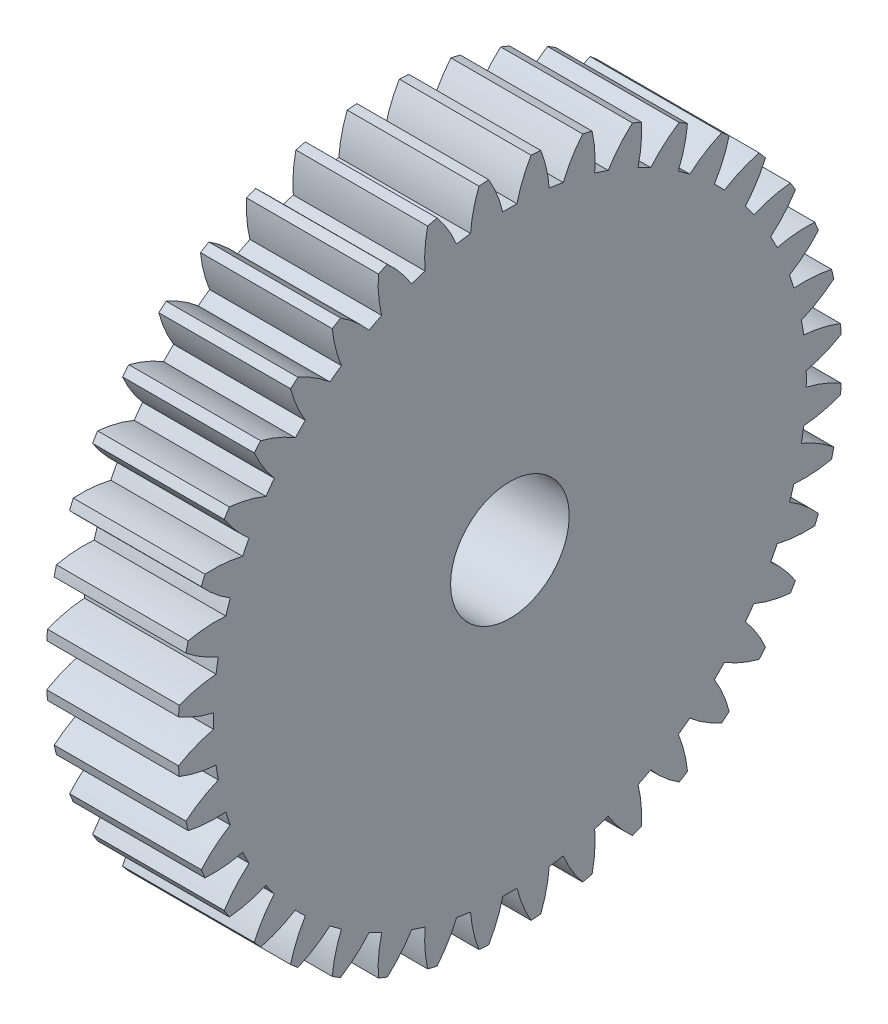
SolidWorks part; units mm, degrees
ref_plane "Plane1" through (0, 0, 0) normal (0, 0, 1) x (1, 0, 0)
ref_plane "Plane2" through (0, 0, 0) normal (0, 1, 0) x (1, 0, 0)
ref_plane "Plane3" through (0, 0, 0) normal (1, 0, 0) x (0, 0, -1)
sketch "HoldingSke" plane through (0, 0, 0) normal (0, 1, 0) x (1, 0, 0)
  line L0 (0, 0) -> (1.2767, -1.0713)
  line L1 (-15, 0) -> (100, 0) construction
  line L2 (0, 0) -> (-2.1039, 2.3779)
  line L3 (0, 0) -> (-11.863, 4.5341)
  line L4 (0, 0) -> (6.6156, 5.5511)
  line L5 (0, 0) -> (-46.8476, -17.4728)
  line L6 (0, 0) -> (-4.1448, -2.7965)
  line L7 (-2.1039, 2.3779) -> (8.6586, 51.2059)
  line L8 (-76.2, 54.61) -> (-76.1, 54.61)
  line L9 (-71.009, 38.7566) -> (-53.1078, 45.2721)
  line L10 (-76.2, 71.12) -> (104.1128, 71.12)
  line L11 (0, 0) -> (-5, 0)
  line L12 (-76.2, 101.6) -> (-76.177, 101.6)
  line L13 (24.9733, 27.94) -> (52.9518, 28.4284)
  line L14 (24.9733, 27.94) -> (24.9743, 27.94)
  line L15 (24.9733, 27.94) -> (100.4006, 29.5858)
  line L16 (-63.627, -0.6) -> (-12.827, -0.6)
  circle A0 centre (0, 0) radius 0.4
  circle A1 centre (0, 0) radius 11.249
  circle A2 centre (0, 0) radius 37.5
  circle A3 centre (0, 0) radius 0.4
  dimension "MHD" = 22.498
  dimension "Hub_dia" = 75
  dimension "Bore" = 0.8
  dimension "MBD" = 0.8
  dimension "Num_teeth" = 40
  dimension "Pitch" = 1.6667
  dimension "Overall_len" = 50
  dimension "Show_teeth" = 40
  dimension "Thickness" = 5
  dimension "OAL" = 50.0001
  dimension "T_dim" = 0.1
  dimension "Ap" = 20
  dimension "H" = 19.05
  dimension "Pitch_radius" = 180.3128
  dimension "Width" = 5
  dimension "Backlash" = 0.023
  dimension "Addendum_fac" = 1
  dimension "Dedendum_fac" = 1.25
  dimension "Clearance_fac" = 0.25
  dimension "Dedendum_add" = 0.001
  dimension "Module" = 0.6
sketch "BasProSke" plane through (0, 0, 0) normal (0, 1, 0) x (1, 0, 0)
  line L0 (-10, 0) -> (60, 0) construction
  line L1 (0, 0) -> (0, 12.6)
  line L2 (0, 0) -> (5, 0)
  line L3 (5, 0) -> (5, 12.6)
  line L4 (5, 12.6) -> (0, 12.6)
  dimension "Thickness" = 5
  dimension "Diameter" = 25.2
revolve "Base-Revolve" add sketch "BasProSke" angle 360 about L0
sketch "TooCutSke" plane through (0, 0, 0) normal (1, 0, 0) x (0, 0, -1)
  line L1 (0, 0) -> (0, 107) construction
  line L2 (0, 0) -> (-0.5114, 11.9891) construction
  line L3 (0, 0) -> (-1.8818, 23.9106) construction
  line L4 (-0.5114, 11.9891) -> (-0.9409, 11.9553) construction
  arc A0 (0.2694, 11.2458) -> (-0.2694, 11.2458) centre (0, 0) ccw
  arc A1 (0.8191, 12.5988) -> (-0.8191, 12.5988) centre (0, 0) ccw
  circle A2 centre (0, 0) radius 12 construction
  circle A3 centre (0, 0) radius 11.2763 construction
  arc A4 (-0.2694, 11.2458) -> (-0.8191, 12.5988) centre (-4.9396, 10.1368) ccw
  arc A5 (0.8191, 12.5988) -> (0.2694, 11.2458) centre (4.9396, 10.1368) ccw
  dimension "Root_dia" = 22.498
  dimension "Overcut_dia" = 25.2508
  dimension "Pitch_dia" = 24
  dimension "Base_dia" = 22.5526
  dimension "Flank_rad" = 4.8
  dimension "Half_ang" = 4.5
  dimension "Half_CT" = 0.4309
extrude "ToothCut" cut sketch "TooCutSke" along normal through all
fillet "Breaks" [suppressed] radius 0.012
fillet "RootFillets" [suppressed] radius 0.151
pattern_circular "TeethCuts" count 40 every 9 about axis through (-10, 0, 0) along (1, 0, 0) of "ToothCut", "RootFillets", "Breaks"
sketch "HubNeaOneSke" plane through (0, 0, 0) normal (-1, 0, 0) x (0, 0, 1)
  circle A0 centre (0, 0) radius 11.249
  dimension "Diameter" = 22.498
extrude "HubNearOne" [suppressed] add sketch "HubNeaOneSke" along normal blind 45.0001
sketch "HubNeaBotSke" plane through (0, 0, 0) normal (-1, 0, 0) x (0, 0, 1)
  circle A0 centre (0, 0) radius 11.249
  dimension "Diameter" = 22.498
extrude "HubNearBoth" [suppressed] add sketch "HubNeaBotSke" along normal blind 22.5
ref_plane "FarPln" through (5, 0, 0) normal (1, 0, 0) x (0, 0, -1)
sketch "HubFarSke" plane through (5, 0, 0) normal (1, 0, 0) x (0, 0, -1)
  circle A0 centre (0, 0) radius 11.249
  dimension "Diameter" = 22.498
extrude "HubFar" [suppressed] add sketch "HubFarSke" along normal blind 22.5
sketch "BorSke" plane through (0, 0, 0) normal (1, 0, 0) x (0, 0, -1)
  circle A0 centre (0, 0) radius 0.4
  dimension "Diameter" = 0.8
extrude "Bore" cut sketch "BorSke" along normal mid plane 100.0001
sketch "KeySke" plane through (0, 0, 0) normal (1, 0, 0) x (0, 0, -1)
  line L0 (-0.05, 0) -> (-0.05, 0.5)
  line L1 (-0.05, 0.5) -> (0.05, 0.5)
  line L2 (0.05, 0.5) -> (0.05, 0)
  line L3 (0, 0) -> (0, 34) construction
  line L4 (-0.05, 0) -> (0.05, 0)
  dimension "Offset" = 0.5
  dimension "Width" = 0.1
extrude "Keyway" [suppressed] cut sketch "KeySke" along normal mid plane 100.0001
pattern_circular "Keyway2" [suppressed] count 2 every 90 about axis through (-10, 0, 0) along (1, 0, 0)
sketch "Sketch1" plane through (0, 0, 0) normal (-1, 0, 0) x (0, 0, 1)
  circle A0 centre (0, 0) radius 2.25
  dimension "D1" = 4.5
extrude "Cut-Extrude1" cut sketch "Sketch1" against normal through all
equation "' \"Module@HoldingSke\" = 6.35"
equation "' \"Num_teeth@HoldingSke\" = 12"
equation "' \"Ap@HoldingSke\" =  20"
equation "' \"Ap@HoldingSke\" = 20"
equation "' \"Width@HoldingSke\" = 0.5 * 25.4"
equation "' \"Hub_dia@HoldingSke\"= 1 * 25.4"
equation "' \"Hub_dia@HoldingSke\" = 1 * 25.4"
equation "' \"Overall_len@HoldingSke\" = 1.0 * 25.4"
equation "' \"Bore@HoldingSke\" = 0.75 * 25.4"
equation "' \"T_dim@HoldingSke\" = 0.1 * 25.4"
equation "' \"Width@KeySke\" = 0.25 * 25.4"
equation "' \"Show_teeth@HoldingSke\" = 13"
equation "' \"Backlash@HoldingSke\" = 0.009 * 25.4"
equation "' \"Addendum_fac@HoldingSke\" = 1.0"
equation "' \"Dedendum_fac@HoldingSke\" = 1.25"
equation "' \"Dedendum_add@HoldingSke\" = 0.00005 * 25.4"
equation "' \"Clearance_fac@HoldingSke\" = 0.25"
equation "\"Pitch@HoldingSke\" = 1 / \"Module@HoldingSke\""
equation "\"Overcut_dia@TooCutSke\" = (\"Num_teeth@HoldingSke\" + 2 * \"Addendum_fac@HoldingSke\") / \"Pitch@HoldingSke\" + 0.002 * 25.4"
equation "\"Pitch_dia@TooCutSke\" = \"Num_teeth@HoldingSke\" / \"Pitch@HoldingSke\""
equation "\"Base_dia@TooCutSke\" = \"Num_teeth@HoldingSke\" / \"Pitch@HoldingSke\" * cos((\"Ap@HoldingSke\"  * 3.14159265 / 180))"
equation "\"Root_dia@TooCutSke\" = (\"Num_teeth@HoldingSke\" + 2) / \"Pitch@HoldingSke\" - 2 * (\"Addendum_fac@HoldingSke\" + \"Dedendum_fac@HoldingSke\") / \"Pitch@HoldingSke\" - \"Dedendum_add@HoldingSke\" * 2"
equation "\"Half_ang@TooCutSke\" = 180 / \"Num_teeth@HoldingSke\""
equation "\"Half_CT@TooCutSke\" = \"Num_teeth@HoldingSke\" / \"Pitch@HoldingSke\" * sin((3.14159265 / 2 / \"Num_teeth@HoldingSke\")) / 2 - 7 * \"Backlash@HoldingSke\" / 4"
equation "\"Flank_rad@TooCutSke\" = \"Num_teeth@HoldingSke\" / \"Pitch@HoldingSke\" / 5"
equation "\"Radius@RootFillets\" = \"Clearance_fac@HoldingSke\" / \"Pitch@HoldingSke\" + \"Dedendum_add@HoldingSke\""
equation "\"Break_rad@Breaks\" = 0.02 / \"Pitch@HoldingSke\""
equation "\"Thickness@HoldingSke\" = \"Width@HoldingSke\""
equation "\"OAL@HoldingSke\" = \"Thickness@HoldingSke\""
equation "\"MHD@HoldingSke\" = (\"Num_teeth@HoldingSke\" + 2) / \"Pitch@HoldingSke\" - 2 * (\"Addendum_fac@HoldingSke\" + \"Dedendum_fac@HoldingSke\")  / \"Pitch@HoldingSke\" - \"Dedendum_add@HoldingSke\" * 2"
equation "\"MBD@HoldingSke\" = (\"Num_teeth@HoldingSke\" + 2) / \"Pitch@HoldingSke\" - 2 * (\"Addendum_fac@HoldingSke\" + \"Dedendum_fac@HoldingSke\")  / \"Pitch@HoldingSke\" - \"Dedendum_add@HoldingSke\" * 2 - 0.002 * 25.4"
equation "\"MHD@HoldingSke\" = ((sgn( \"MHD@HoldingSke\" - \"Hub_dia@HoldingSke\" )-1)*( \"MHD@HoldingSke\" - \"Hub_dia@HoldingSke\" ))/-2+ \"Hub_dia@HoldingSke\""
equation "\"MBD@HoldingSke\" = ((sgn( \"MBD@HoldingSke\" - \"Bore@HoldingSke\" )-1)*( \"MBD@HoldingSke\" - \"Bore@HoldingSke\" ))/-2+ \"Bore@HoldingSke\""
equation "\"OAL@HoldingSke\" = ((sgn( \"OAL@HoldingSke\" - \"Overall_len@HoldingSke\" )+1)*( \"OAL@HoldingSke\" - \"Overall_len@HoldingSke\" ))/2 + \"Overall_len@HoldingSke\" + 0.000002 * 25.4"
equation "\"Num_teeth@TeethCuts\" = int( \"Show_teeth@HoldingSke\" ) + 1"
equation "\"Num_teeth@TeethCuts\" = ((sgn( \"Num_teeth@TeethCuts\" - \"Num_teeth@HoldingSke\" )-1)*( \"Num_teeth@TeethCuts\" - \"Num_teeth@HoldingSke\" ))/-2+ \"Num_teeth@HoldingSke\""
equation "\"Num_teeth@TeethCuts\" = ((sgn( \"Num_teeth@TeethCuts\" - 2.0)+1)*( \"Num_teeth@TeethCuts\" - 2.0))/2 +2.0"
equation "\"Angle@TeethCuts\" = 360.0 / \"Num_teeth@HoldingSke\""
equation "\"Diameter@BasProSke\" = (\"Num_teeth@HoldingSke\" + 2 * \"Addendum_fac@HoldingSke\") / \"Pitch@HoldingSke\""
equation "\"Thickness@BasProSke\"  = \"Thickness@HoldingSke\""
equation "' \"Fillet_rad@BasProSke\" =  \"Thickness@HoldingSke\" * 0.05"
equation "' \"Fillet_rad@BasProSke\" = \"Thickness@HoldingSke\" * 0.05"
equation "\"MHD@HoldingSke\" = ((sgn( \"MHD@HoldingSke\" - \"Root_dia@TooCutSke\" )-1)*( \"MHD@HoldingSke\" - \"Root_dia@TooCutSke\" ))/-2+ \"Root_dia@TooCutSke\""
equation "\"Diameter@HubNeaOneSke\" = \"MHD@HoldingSke\""
equation "\"Length@HubNearOne\" = \"OAL@HoldingSke\" - \"Thickness@BasProSke\""
equation "\"Diameter@HubNeaBotSke\" = \"MHD@HoldingSke\""
equation "\"Length@HubNearBoth\" = ( \"OAL@HoldingSke\" - \"Thickness@BasProSke\" ) / 2.0"
equation "\"Thickness@FarPln\" = \"Thickness@BasProSke\""
equation "\"Diameter@HubFarSke\" = \"MHD@HoldingSke\""
equation "\"Length@HubFar\" = ( \"OAL@HoldingSke\" - \"Thickness@BasProSke\" ) / 2.0"
equation "\"Diameter@BorSke\" = \"MBD@HoldingSke\""
equation "\"D1@Bore\" = \"OAL@HoldingSke\" * 2.0"
equation "\"D1@Keyway\" = \"OAL@HoldingSke\" * 2.0"
equation "\"Offset@KeySke\" = \"T_dim@HoldingSke\" + \"MBD@HoldingSke\" / 2.0"
